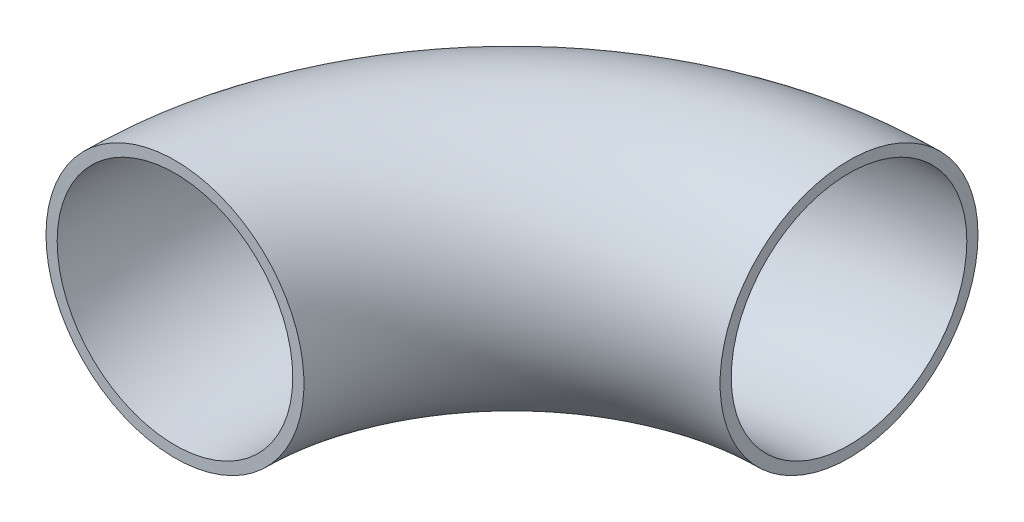
SolidWorks part; units mm, degrees
ref_plane "Front Plane" through (0, 0, 0) normal (0, 0, 1) x (1, 0, 0)
ref_plane "Top Plane" through (0, 0, 0) normal (0, 1, 0) x (1, 0, 0)
ref_plane "Right Plane" through (0, 0, 0) normal (1, 0, 0) x (0, 0, -1)
sketch "Sketch2" plane through (0, 0, 0) normal (0, 1, 0) x (1, 0, 0)
  arc A0 (0, 49.784) -> (-49.784, 0) centre (0, 0) ccw
  point P0 (0, 49.784)
  point P1 (-49.784, 0)
ref_plane "Plane2" through (0, 0, -49.784) normal (-1, 0, 0) x (0, 0, 1)
sketch "Sketch6" plane through (0, 0, -49.784) normal (-1, 0, 0) x (0, 0, 1)
  circle A0 centre (0, 0) radius 19.05
sweep "Sweep-Thin1" add profiles "Sketch6" path "Sketch2" parameters "D1"=1.651
